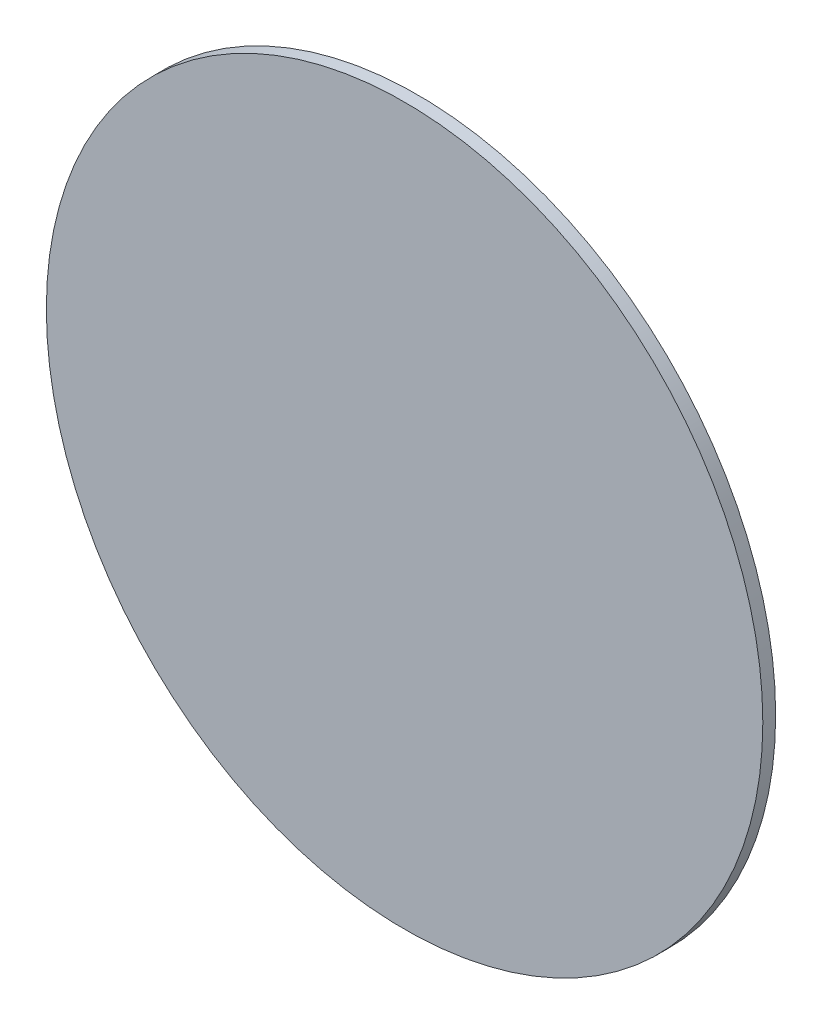
SolidWorks part; units mm, degrees
material "6063-O"
ref_plane "Front Plane" through (0, 0, 0) normal (0, 0, 1) x (1, 0, 0)
ref_plane "Top Plane" through (0, 0, 0) normal (0, 1, 0) x (1, 0, 0)
ref_plane "Right Plane" through (0, 0, 0) normal (1, 0, 0) x (0, 0, -1)
sketch "Sketch1" plane through (0, 0, 0) normal (0, 0, 1) x (1, 0, 0)
  line L0 (-10638.6301, 9168.8113) -> (-10718.6301, 9168.8113) construction
  circle A0 centre (-10678.6301, 9168.8113) radius 278.8965
extrude "Boss-Extrude1" add sketch "Sketch1" along normal blind 10
